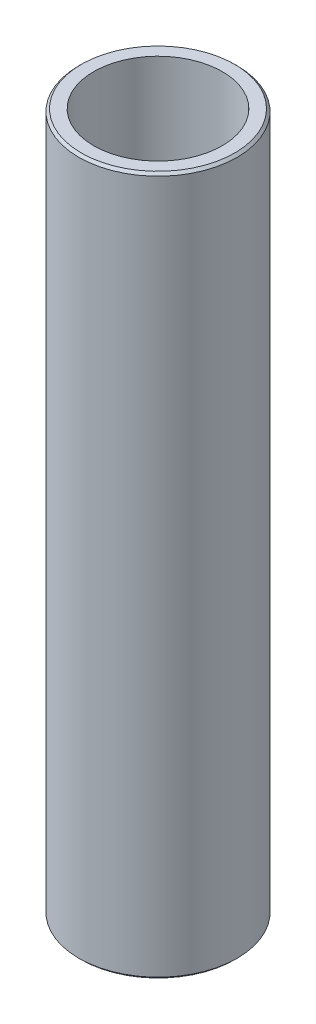
SolidWorks part; units mm, degrees
ref_plane "Front Plane" through (0, 0, 0) normal (0, 0, 1) x (1, 0, 0)
ref_plane "Top Plane" through (0, 0, 0) normal (0, 1, 0) x (1, 0, 0)
ref_plane "Right Plane" through (0, 0, 0) normal (1, 0, 0) x (0, 0, -1)
sketch "Sketch1" plane through (0, 0, 0) normal (0, 1, 0) x (1, 0, 0)
  circle A0 centre (0, 0) radius 7.94
  circle A1 centre (0, 0) radius 6.44
  dimension "D1" = 15.88
  dimension "D2" = 1.5
extrude "Boss-Extrude1" add sketch "Sketch1" along normal blind 70
chamfer "Chamfer1" distance 0.25 angle 45 2 edges at (0, 0, 7.94) (0, 70, 7.94)
